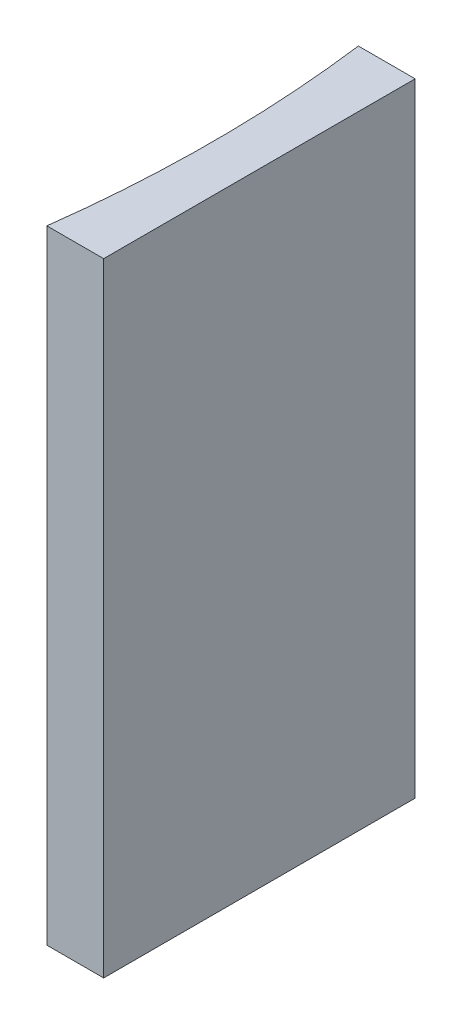
SolidWorks part; units mm, degrees
ref_plane "前视基准面" through (0, 0, 0) normal (0, 0, 1) x (1, 0, 0)
ref_plane "上视基准面" through (0, 0, 0) normal (0, 1, 0) x (1, 0, 0)
ref_plane "右视基准面" through (0, 0, 0) normal (1, 0, 0) x (0, 0, -1)
sketch "草图1" plane through (0, 0, 0) normal (0, 1, 0) x (1, 0, 0)
  line L0 (0, 0) -> (0, -20)
  line L1 (0, 0) -> (-3.6474, 0)
  line L2 (0, -20) -> (-3.6474, -20)
  line L3 (8.2336, -10) -> (-10.4405, -10) construction
  arc A0 (-3.6474, -20) -> (-3.6474, 0) centre (-80.55, -10) ccw
  point P7 (-3, -10)
  point P8 (0, -10)
  dimension "D2" = 77.55
  dimension "D3" = 3
  dimension "D1" = 20
extrude "凸台-拉伸1" add sketch "草图1" along normal blind 40
